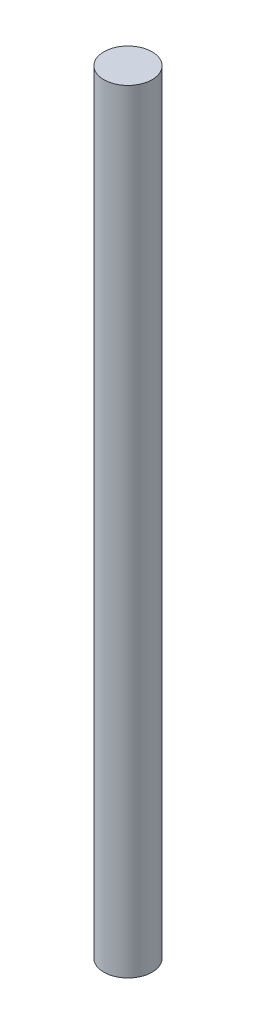
SolidWorks part; units mm, degrees
ref_plane "Front Plane" through (0, 0, 0) normal (0, 0, 1) x (1, 0, 0)
ref_plane "Top Plane" through (0, 0, 0) normal (0, 1, 0) x (1, 0, 0)
ref_plane "Right Plane" through (0, 0, 0) normal (1, 0, 0) x (0, 0, -1)
sketch "Sketch1" plane through (0, 0, 0) normal (0, 1, 0) x (1, 0, 0)
  circle A0 centre (0, 0) radius 2.3813
  dimension "D1" = 4.7625
extrude "Boss-Extrude1" add sketch "Sketch1" along normal blind 76.2
